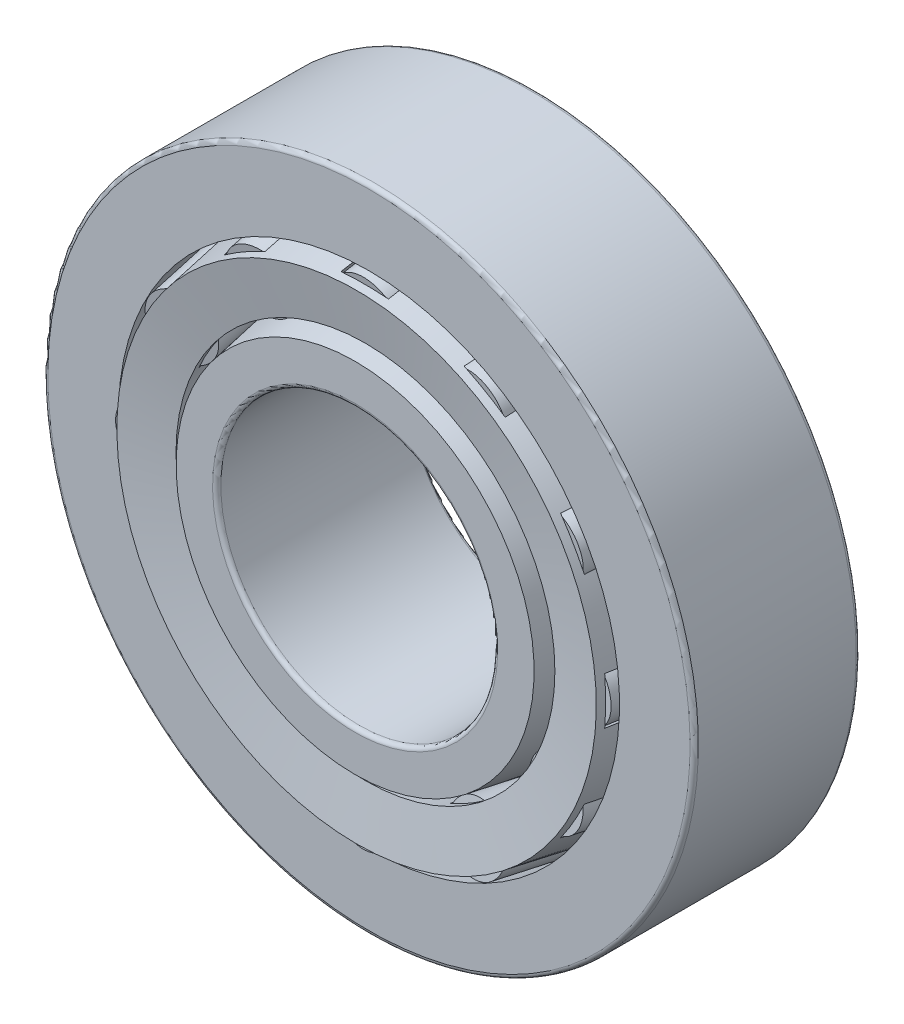
SolidWorks part; units mm, degrees
ref_plane "Front Plane" through (0, 0, 0) normal (0, 0, 1) x (1, 0, 0)
ref_plane "Top Plane" through (0, 0, 0) normal (0, 1, 0) x (1, 0, 0)
ref_plane "Right Plane" through (0, 0, 0) normal (1, 0, 0) x (0, 0, -1)
sketch "Sketch1" plane through (0, 0, 0) normal (1, 0, 0) x (0, 0, -1)
  line L0 (-7, 0) -> (7, 0) construction
  line L1 (0, 0) -> (0, 23.5) construction
  line L2 (-7, 10) -> (7, 10) construction
  line L3 (7, 10) -> (7, 15.4) construction
  line L4 (7, 15.4) -> (-7, 12.9314) construction
  line L5 (-7, 12.9314) -> (-7, 10) construction
  line L7 (-6, 23.5) -> (6, 23.5)
  line L8 (6, 23.5) -> (6, 20.2159)
  line L9 (6, 20.2159) -> (-6, 18.1)
  line L10 (-6, 18.1) -> (-6, 23.5)
  line L12 (7.3963, 20.4621) -> (8.25, 15.6204) construction
  line L13 (-6.1463, 13.082) -> (-7, 17.9237) construction
  line L14 (-7, 12.9314) -> (-6.1463, 13.082) construction
  line L15 (-7, 12.9314) -> (8.25, 15.6204) construction
  line L20 (-7, -12.9314) -> (8.25, -15.6204) construction
  line L21 (-7, -12.9314) -> (-6.1463, -13.082) construction
  line L22 (-6.1463, -13.082) -> (-7, -17.9237) construction
  line L23 (7.3963, -20.4621) -> (8.25, -15.6204) construction
  line L24 (-7, -12.9314) -> (-7, -10) construction
  line L25 (7, -15.4) -> (-7, -12.9314) construction
  line L26 (7, -10) -> (7, -15.4) construction
  line L27 (-7, -10) -> (7, -10) construction
  line L28 (-6, -18.1) -> (-6, -23.5) construction
  line L29 (6, -20.2159) -> (-6, -18.1) construction
  line L30 (6, -23.5) -> (6, -20.2159) construction
  line L31 (-6, -23.5) -> (6, -23.5) construction
  point P5 (0, 10)
  point P37 (0, -10)
  dimension "Width" = 14
  dimension "OD" = 47
  dimension "Shaft Dia" = 20
  dimension "D1" = 100
  dimension "D2" = 13.5
  dimension "D3" = 5.4
  dimension "Outer Wd" = 12
  dimension "Bearing Wd" = 15.25
revolve "Revolve1" add sketch "Sketch1" angle 360 about L0
sketch "Sketch5" plane through (0, 0, 0) normal (1, 0, 0) x (0, 0, -1)
  line L0 (7, 15.4) -> (-7, 12.9314) construction
  line L1 (7, 15.4) -> (-7, 12.9314)
  line L2 (-7, 12.9314) -> (-7, 10)
  line L3 (-7, 10) -> (7, 10)
  line L4 (7, 10) -> (7, 15.4)
revolve "Revolve4" add sketch "Sketch5" angle 360 about L0
sketch "Sketch2" plane through (0, 0, 0) normal (1, 0, 0) x (0, 0, -1)
  line L0 (-6.8933, 17.3185) -> (-6.253, 13.6872)
  line L1 (6, 19.5919) -> (7.503, 19.8569)
  line L2 (-6.253, 13.6872) -> (6, 15.8477)
  line L3 (7.3963, 20.4621) -> (8.25, 15.6204) construction
  line L4 (6, 15.8477) -> (6, 19.5919) construction
  line L5 (6, 19.5919) -> (-6.8933, 17.3185)
  line L6 (6, 20.2159) -> (-6, 18.1) construction
  line L7 (7, 15.4) -> (-7, 12.9314) construction
  line L8 (-7, 17.9237) -> (6, 20.2159) construction
  line L9 (-6.1463, 13.082) -> (8.25, 15.6204) construction
  line L10 (7.503, 19.8569) -> (8.1433, 16.2256)
  line L11 (-7, 17.9237) -> (-6.8933, 17.3185) construction
  line L12 (6, -23.5) -> (6, 23.5) construction
  line L13 (6, 23.5) -> (6, 20.2159) construction
  line L14 (8.1433, 16.2256) -> (6, 15.8477)
  line L15 (-6.253, 13.6872) -> (-6.1463, 13.082) construction
  line L16 (0, 0) -> (-7, 0) construction
  line L17 (-7, 12.9314) -> (-7, -12.9314) construction
  line L18 (-6.253, -13.6872) -> (-6.1463, -13.082) construction
  line L19 (-7, -17.9237) -> (-6.8933, -17.3185) construction
  line L20 (-6.1463, -13.082) -> (8.25, -15.6204) construction
  line L21 (-7, -17.9237) -> (6, -20.2159) construction
  line L22 (6, -15.8477) -> (6, -19.5919) construction
  line L23 (8.1433, -16.2256) -> (6, -15.8477) construction
  line L24 (7.503, -19.8569) -> (8.1433, -16.2256) construction
  line L25 (6, -19.5919) -> (-6.8933, -17.3185) construction
  line L26 (-6.253, -13.6872) -> (6, -15.8477) construction
  line L27 (6, -19.5919) -> (7.503, -19.8569) construction
  line L28 (-6.8933, -17.3185) -> (-6.253, -13.6872) construction
  dimension "D2" = 3.6873
  dimension "D1" = 4.9164
revolve "Revolve2" add sketch "Sketch2" angle 360 about L0
sketch "Sketch3" plane through (0, 0, 0) normal (1, 0, 0) x (0, 0, -1)
  line L0 (-6.5731, 15.5028) -> (6, 17.7198) construction
  line L1 (-6.8933, 17.3185) -> (-6.253, 13.6872) construction
  line L2 (6, 15.8477) -> (6, 19.5919) construction
  line L3 (-6, 15.6039) -> (-6.4269, 18.0247)
  line L5 (-6.4269, 18.0247) -> (5.5731, 20.1407)
  line L6 (5.5731, 20.1407) -> (6, 17.7198)
  line L7 (6, 17.7198) -> (-6, 15.6039)
  line L11 (-6.5731, 15.5028) -> (-6, 15.6039) construction
  line L12 (-6, 23.5) -> (-6, -23.5) construction
  line L13 (-6.5731, 15.5028) -> (-6, 15.6039) construction
revolve "Cut-Revolve1" cut sketch "Sketch3" angle 360 about L0
sketch "Sketch4" plane through (0, 0, 0) normal (1, 0, 0) x (0, 0, -1)
  line L0 (-6.4048, 17.8997) -> (5.5952, 20.0156)
  line L1 (5.5952, 20.0156) -> (6, 17.7198)
  line L2 (6, 17.7198) -> (-6, 15.6039)
  line L3 (-6, 15.6039) -> (-6.5731, 15.5028) construction
  line L4 (-6, 15.6039) -> (-6.4048, 17.8997)
  line L5 (-6.5731, 15.5028) -> (-6, 15.6039) construction
  line L6 (6, 17.7198) -> (-6, 15.6039) construction
  line L7 (6, 20.2159) -> (-6, 18.1) construction
  line L8 (0, 0) -> (-7, 0) construction
  line L9 (-7, 0) -> (7, 0) construction
  line L10 (-6.5731, -15.5028) -> (-6, -15.6039) construction
  line L11 (-6, -15.6039) -> (-6.5731, -15.5028) construction
  line L12 (-6, -15.6039) -> (-6.4048, -17.8997) construction
  line L13 (6, -17.7198) -> (-6, -15.6039) construction
  line L14 (5.5952, -20.0156) -> (6, -17.7198) construction
  line L15 (-6.4048, -17.8997) -> (5.5952, -20.0156) construction
  dimension "D1" = 0.127
revolve "Revolve3" add sketch "Sketch4" angle 360 about L0
ref_axis "Axis1" through (0, 0, -7) along (0, 0, 1)
pattern_circular "CirPattern1" count 12 every 30 about axis through (0, 0, 0) along (0, 0, 1) of "Cut-Revolve1"
pattern_circular "CirPattern2" count 12 every 30 about axis through (0, 0, -7) along (0, 0, 1) of bodies 403
fillet "Fillet1" radius 0.3 2 edges at (0, -23.5, -6) (0, -23.5, 6)
fillet "Fillet2" radius 0.3 2 edges at (0, -10, -7) (0, -10, 7)
sketch "Sketch6" plane through (0, 0, 0) normal (1, 0, 0) x (0, 0, -1)
  line L0 (-43.8933, 23.5) -> (-43.8933, 18.1)
  line L1 (-43.8933, 18.1) -> (-31.8933, 20.2159)
  line L2 (-31.8933, 20.2159) -> (-31.8933, 23.5)
  line L3 (-31.8933, 23.5) -> (-43.8933, 23.5)
  line L4 (-6, 23.5) -> (6, 23.5) construction
  line L5 (6, 23.5) -> (6, 20.2159) construction
  line L6 (6, 20.2159) -> (-6, 18.1) construction
  line L7 (-6.8933, -17.3185) -> (-6.8933, 17.3185) construction
  dimension "D1" = 25
revolve "Revolve5" [suppressed] add sketch "Sketch6" angle 360 about L0
fillet "Fillet3" [suppressed] radius 0.3
delete or keep bodies "Body-Delete1" [suppressed] type delete bodies bodies 399
equation "\"D3@Sketch1\" = \"D2@Sketch1\"/2.5"
equation "\"D2@Sketch2\" = \"D1@Sketch2\"*.75"
equation "\"Rollers@CirPattern2\" = \"OD@Sketch1\"*.25"
equation "\"Angle@CirPattern2\" = 360/\"Rollers@CirPattern2\""
equation "\"D1@CirPattern1\" = \"Rollers@CirPattern2\""
equation "\"D2@CirPattern1\" = \"Angle@CirPattern2\""
equation "\"D1@Fillet1\" = \"Outer Wd@Sketch1\"*.025"
equation "\"D1@Fillet2\" = \"D1@Fillet1\""
equation "\"D1@Fillet3\" = \"D1@Fillet1\""
